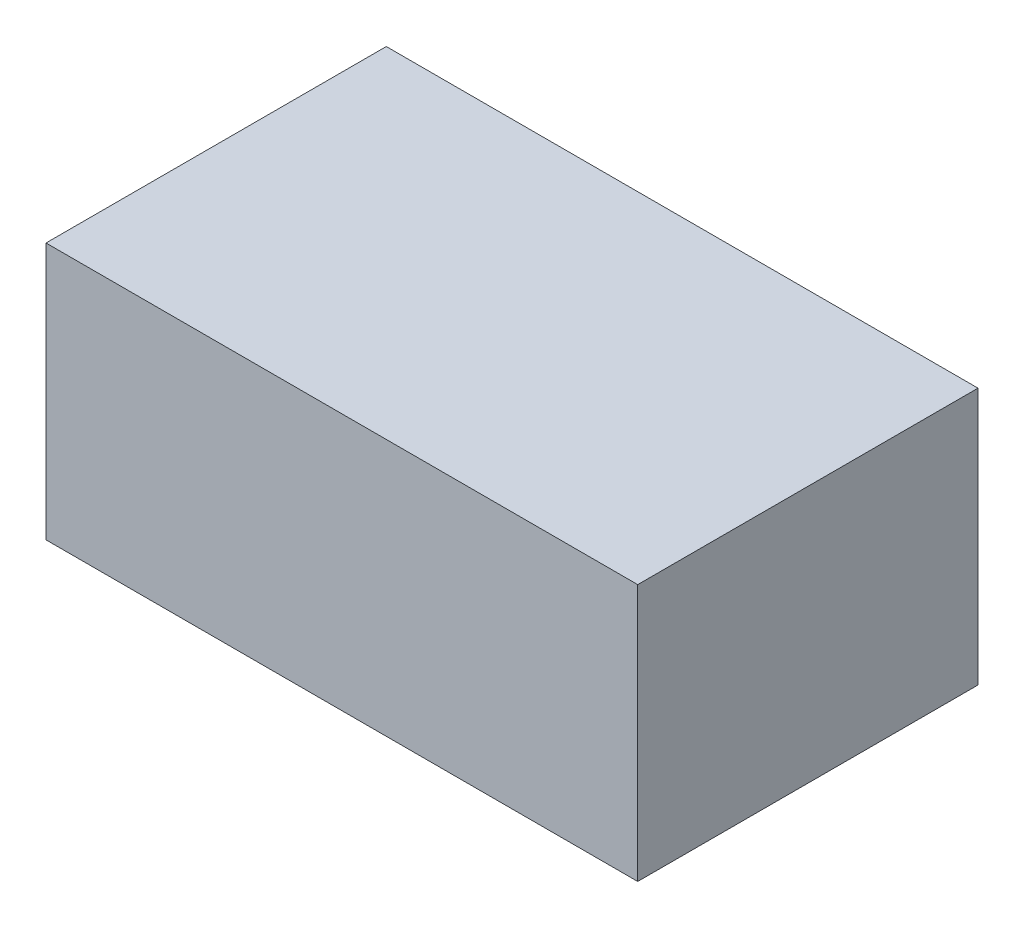
SolidWorks part; units mm, degrees
ref_plane "Front Plane" through (0, 0, 0) normal (0, 0, 1) x (1, 0, 0)
ref_plane "Top Plane" through (0, 0, 0) normal (0, 1, 0) x (1, 0, 0)
ref_plane "Right Plane" through (0, 0, 0) normal (1, 0, 0) x (0, 0, -1)
other "Bounding Box"
ref_plane "Default Plane" through (13.8565, 3.175, 6.7999) normal (0, -1, 0) x (-1, 0, 0)
sketch "Sketch1" plane through (0, 0, 0) normal (0, 1, 0) x (1, 0, 0)
  line L1 (-19.8755, 11.43) -> (19.8755, 11.43)
  line L2 (-19.8755, 11.43) -> (-19.8755, -11.43)
  line L3 (-19.8755, -11.43) -> (19.8755, -11.43)
  line L4 (19.8755, 11.43) -> (19.8755, -11.43)
  line L5 (-19.8755, 11.43) -> (19.8755, -11.43) construction
  line L6 (-19.8755, -11.43) -> (19.8755, 11.43) construction
  point P0 (0, 0)
  dimension "D1" = 39.751
  dimension "D2" = 22.86
extrude "Boss-Extrude1" add sketch "Sketch1" along normal mid plane 17.272
